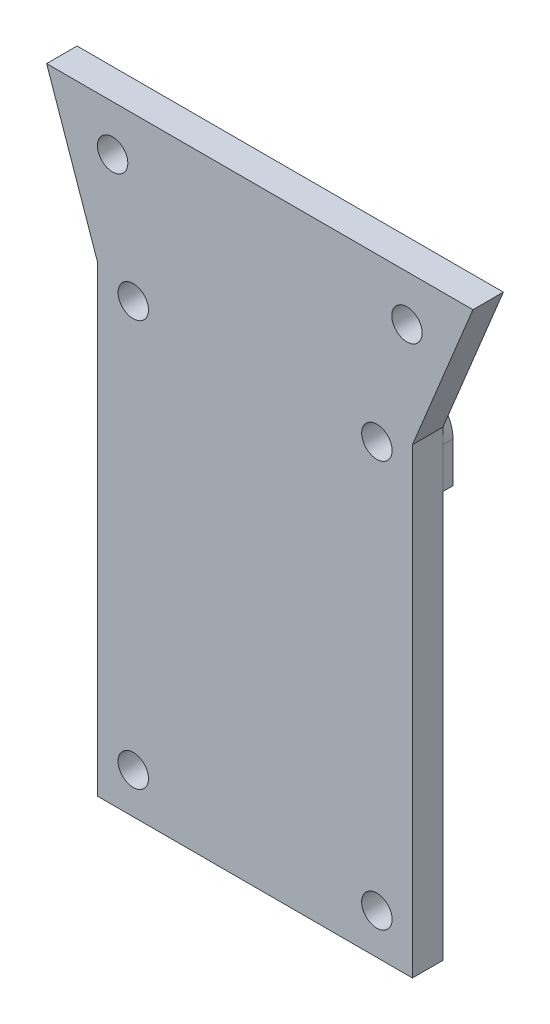
SolidWorks part; units mm, degrees
ref_plane "Front Plane" through (0, 0, 0) normal (0, 0, 1) x (1, 0, 0)
ref_plane "Top Plane" through (0, 0, 0) normal (0, 1, 0) x (1, 0, 0)
ref_plane "Right Plane" through (0, 0, 0) normal (1, 0, 0) x (0, 0, -1)
sketch "Sketch1" plane through (0, 0, 0) normal (0, 0, 1) x (1, 0, 0)
  line L1 (0, 0) -> (31, 0)
  line L2 (0, 0) -> (0, 45.5)
  line L3 (-5.037, 60) -> (36.963, 60)
  line L4 (31, 0) -> (31, 45.5)
  line L5 (36.963, 60) -> (31, 45.5)
  line L7 (-5.037, 60) -> (0, 45.5)
  circle A0 centre (30.463, 55.5) radius 1.5
  circle A1 centre (27.5, 44) radius 1.5
  circle A4 centre (27.5, 4) radius 1.5
  circle A5 centre (3.5, 4) radius 1.5
  circle A7 centre (3.5, 44) radius 1.5
  circle A9 centre (1.463, 55.5) radius 1.5
  point P29 (15.963, 60)
  dimension "D4" = 3
  dimension "D5" = 21
  dimension "D6" = 2
  dimension "D7" = 2
  dimension "D8" = 21
  dimension "D9" = 2.5
  dimension "D10" = 37
  dimension "D11" = 2.8
  dimension "D12" = 29
  dimension "D13" = 14.5
  dimension "D14" = 11.5
  dimension "D15" = 3
  dimension "D16" = 5
  dimension "D2" = 0
  dimension "D3" = 31
extrude "Boss-Extrude1" add sketch "Sketch1" along normal blind 3
sketch "Sketch2" plane through (0, 0, 0) normal (0, 0, -1) x (-1, 0, 0)
  line L1 (0, 44) -> (0, 19)
  line L3 (0, 45.5) -> (0, 0) construction
  line L4 (0, 19) -> (-11, 19)
  line L7 (-18, 43.5) -> (-18, 21)
  line L8 (-31, 44) -> (-31, 40)
  line L9 (-31, 0) -> (-31, 45.5) construction
  line L10 (-20, 19) -> (-24, 19)
  line L11 (-24, 26.2797) -> (-24, 11.7203) construction
  line L12 (-36.4403, 40) -> (-25.5597, 40) construction
  line L13 (-13, 21) -> (-13, 43.5)
  line L14 (-13, 43.5) -> (-8.7915, 43.5)
  line L15 (-18, 43.5) -> (-22.2085, 43.5)
  circle A0 centre (-3.5, 44) radius 1.5 construction
  circle A1 centre (-27.5, 44) radius 1.5 construction
  circle A2 centre (-3.5, 44) radius 1.5 construction
  circle A3 centre (-27.5, 44) radius 1.5 construction
  circle A4 centre (-27.5, 44) radius 2.5
  circle A5 centre (-3.5, 44) radius 2.5
  arc A6 (0, 44) -> (-6.8673, 44.9545) centre (-3.5, 44) ccw
  arc A7 (-24.1327, 44.9545) -> (-31, 44) centre (-27.5, 44) ccw
  arc A8 (-11, 19) -> (-13, 21) centre (-11, 21) cw
  arc A9 (-18, 21) -> (-20, 19) centre (-20, 21) cw
  arc A10 (-8.7915, 43.5) -> (-6.8673, 44.9545) centre (-8.7915, 45.5) ccw
  arc A11 (-22.2085, 43.5) -> (-24.1327, 44.9545) centre (-22.2085, 45.5) cw
  spline S0 degree 3 poles (-24, 19) (-24, 25.6667) (-24.3333, 40) (-31, 40) knots 0 0 0 0 1 1 1 1
  dimension "D1" = 5
  dimension "D2" = 7
  dimension "D3" = 5
  dimension "D4" = 7
  dimension "D6" = 25
  dimension "D9" = 2
  dimension "D10" = 20
  dimension "D11" = 20
  dimension "D14" = 2
  dimension "D8" = 2
  dimension "D16" = 2
  dimension "D5" = 25
  dimension "D7" = 13
  dimension "D12" = 4
  dimension "D13" = 4
  dimension "D15" = 13
extrude "Boss-Extrude2" add sketch "Sketch2" along normal blind 1 separate body contours L7 A9 L10 S0 L8 A7 L15
sketch "Sketch3" plane through (0, 0, -1) normal (0, 0, -1) x (-1, 0, 0)
  line L0 (0, 44) -> (0, 25.5)
  line L1 (0, 19) -> (0, 44) construction
  line L2 (0, 25.5) -> (-2, 25.5)
  line L3 (-2, 42) -> (-2, 27.5)
  line L6 (-11, 19) -> (0, 19)
  line L7 (0, 19) -> (0, 44)
  line L13 (-2, 27.5) -> (-4, 27.5)
  line L14 (-4, 27.5) -> (-4, 19.5)
  line L15 (-4, 19.5) -> (-2, 19.5)
  line L16 (-2, 19.5) -> (-2, 25.5)
  line L22 (-13, 41.5) -> (-5, 41.5)
  line L23 (-5, 41.5) -> (-5, 42)
  line L26 (-8.7915, 43.5) -> (-13, 43.5)
  line L27 (-8.7915, 43.5) -> (-13, 43.5)
  line L28 (-13, 43.5) -> (-13, 21)
  line L29 (-13, 43.5) -> (-13, 41.5)
  circle A0 centre (-3.5, 44) radius 2.5 construction
  arc A1 (-2, 42) -> (-5, 42) centre (-3.5, 44) ccw
  arc A2 (0, 44) -> (-6.8673, 44.9545) centre (-3.5, 44) ccw
  arc A3 (-13, 21) -> (-11, 19) centre (-11, 21) ccw
  arc A4 (0, 44) -> (-6.8673, 44.9545) centre (-3.5, 44) ccw
  arc A9 (-8.7915, 43.5) -> (-6.8673, 44.9545) centre (-8.7915, 45.5) ccw
  arc A10 (-8.7915, 43.5) -> (-6.8673, 44.9545) centre (-8.7915, 45.5) ccw
  point P17 (-5.7459, 42.9018)
  dimension "D8" = 14
  dimension "D9" = 22
  dimension "D2" = 8
  dimension "D3" = 2
  dimension "D4" = 2
  dimension "D5" = 2
  dimension "D6" = 4
  dimension "D7" = 2
  dimension "D1" = 0
extrude "Boss-Extrude3" add sketch "Sketch3" along normal blind 4 contours L22 L23 A1 L3 L13 L14 L15 L16 L2 L0 A4 A10 L27 L29
sketch "Sketch4" plane through (13, 0, 0) normal (1, 0, 0) x (0, 0, -1)
  line L0 (5, 43.5) -> (5, 41.5)
  line L1 (5, 41.5) -> (1, 41.5)
  line L2 (1, 41.5) -> (1, 43.5)
  line L3 (5, 43.5) -> (0, 43.5) construction
  line L4 (5, 43.5) -> (0, 43.5) construction
  line L5 (1, 43.5) -> (5, 43.5)
extrude "Boss-Extrude4" add sketch "Sketch4" along normal blind 8
